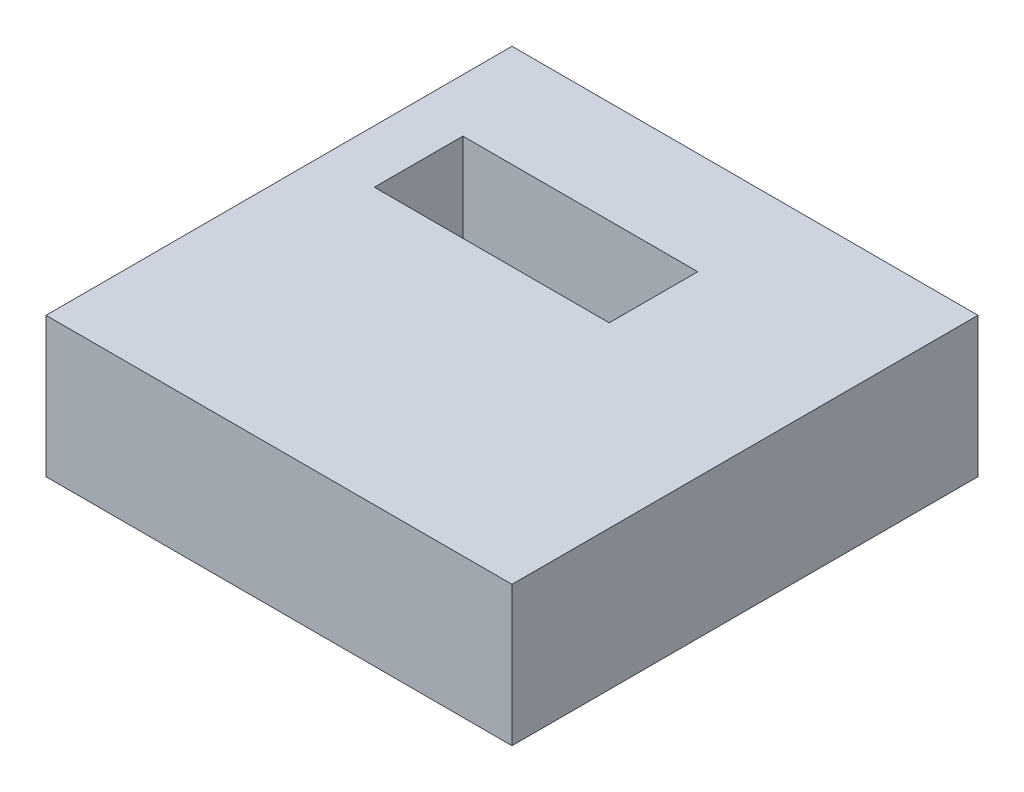
SolidWorks part; units mm, degrees
ref_plane "Front Plane" through (0, 0, 0) normal (0, 0, 1) x (1, 0, 0)
ref_plane "Top Plane" through (0, 0, 0) normal (0, 1, 0) x (1, 0, 0)
ref_plane "Right Plane" through (0, 0, 0) normal (1, 0, 0) x (0, 0, -1)
sketch "Sketch1" plane through (0, 0, 0) normal (0, 1, 0) x (1, 0, 0)
  line L1 (-50, -50) -> (50, -50)
  line L2 (-50, -50) -> (-50, 50)
  line L3 (-50, 50) -> (50, 50)
  line L4 (50, -50) -> (50, 50)
  line L5 (-50, -50) -> (50, 50) construction
  line L6 (-50, 50) -> (50, -50) construction
  line L9 (-38.57, 28.03) -> (11.83, 28.03)
  line L10 (-38.57, 28.03) -> (-38.57, 9.03)
  line L11 (-38.57, 9.03) -> (11.83, 9.03)
  line L12 (11.83, 28.03) -> (11.83, 9.03)
  point P0 (0, 0)
  dimension "D1" = 100
  dimension "D2" = 100
  dimension "D5" = 50.4
  dimension "D6" = 19
extrude "Boss-Extrude1" add sketch "Sketch1" along normal blind 30
